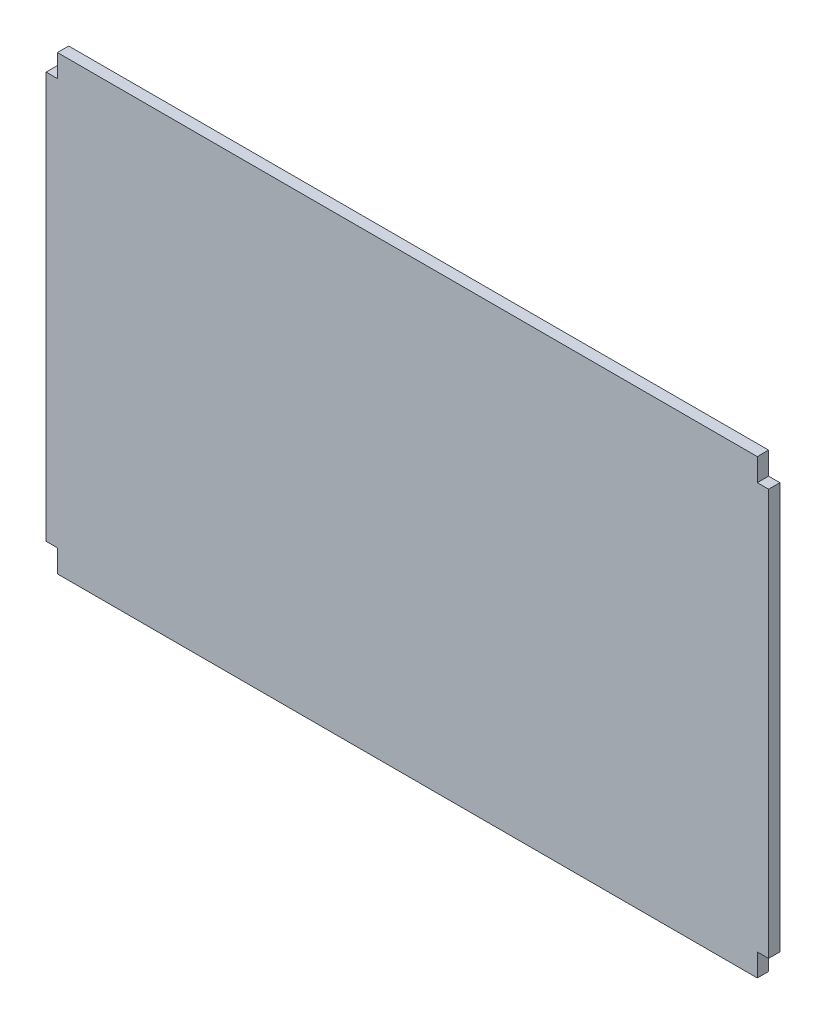
SolidWorks part; units mm, degrees
ref_plane "Front" through (0, 0, 0) normal (0, 0, 1) x (1, 0, 0)
ref_plane "Top" through (0, 0, 0) normal (0, 1, 0) x (1, 0, 0)
ref_plane "Right" through (0, 0, 0) normal (1, 0, 0) x (0, 0, -1)
sketch "Sketch2" plane through (0, 0, 0) normal (0, 0, 1) x (1, 0, 0)
  line L0 (0, 120.65) -> (0, 127)
  line L1 (0, 0) -> (196.85, 0)
  line L2 (0, 0) -> (0, 6.35)
  line L3 (0, 127) -> (196.85, 127)
  line L4 (196.85, 0) -> (196.85, 6.35)
  line L5 (0, 6.35) -> (-3.175, 6.35)
  line L7 (0, 120.65) -> (-3.175, 120.65)
  line L8 (-3.175, 6.35) -> (-3.175, 120.65)
  line L9 (196.85, 6.35) -> (200.025, 6.35)
  line L11 (196.85, 120.65) -> (200.025, 120.65)
  line L12 (200.025, 6.35) -> (200.025, 120.65)
  line L13 (196.85, 120.65) -> (196.85, 127)
  dimension "D1" = 127
  dimension "D2" = 196.85
  dimension "D3" = 3.175
  dimension "D4" = 3.175
  dimension "D5" = 114.3
  dimension "D6" = 114.3
  dimension "D7" = 6.35
  dimension "D8" = 6.35
extrude "Boss-Extrude1" add sketch "Sketch2" along normal blind 3.175
